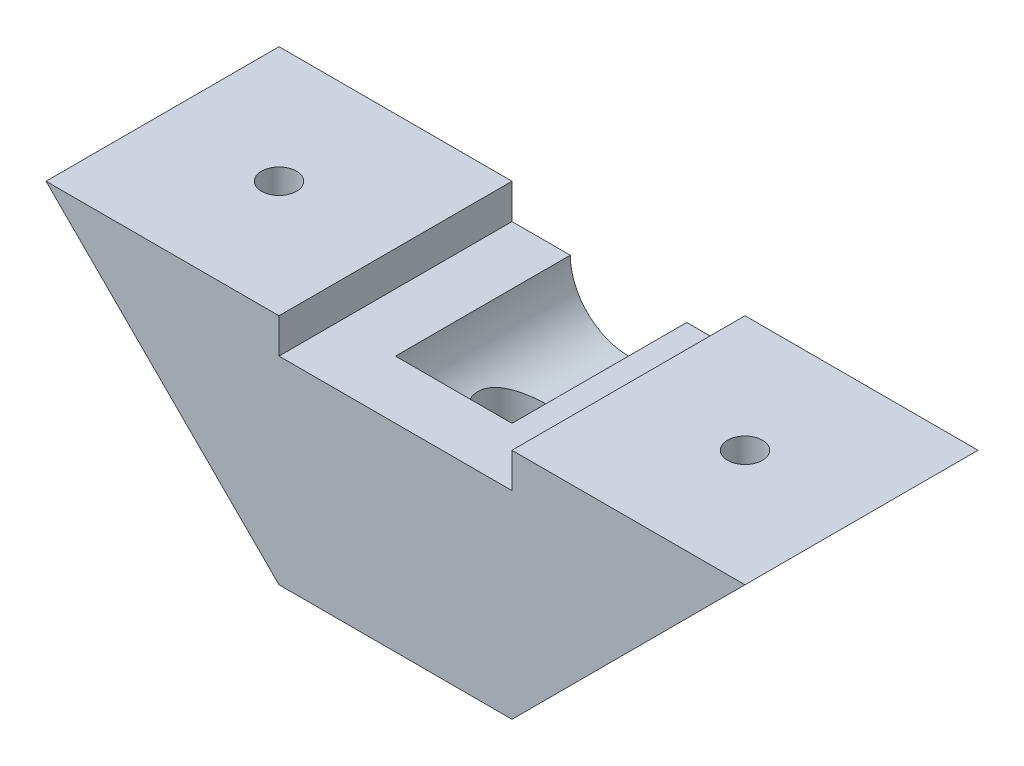
SolidWorks part; units mm, degrees
ref_plane "Plan de face" through (0, 0, 0) normal (0, 0, 1) x (1, 0, 0)
ref_plane "Plan de dessus" through (0, 0, 0) normal (0, 1, 0) x (1, 0, 0)
ref_plane "Plan de droite" through (0, 0, 0) normal (1, 0, 0) x (0, 0, -1)
sketch "Esquisse1" plane through (0, 0, 0) normal (0, 0, 1) x (1, 0, 0)
  line L0 (0, 20) -> (20, 0)
  line L1 (0, 0) -> (60, 0)
  line L2 (0, 0) -> (0, 60)
  line L3 (0, 60) -> (60, 60)
  line L4 (60, 0) -> (60, 60)
  line L5 (0, 0) -> (20, 0)
  line L6 (0, 0) -> (0, 20)
  line L7 (0, 20) -> (20, 20)
  line L8 (20, 0) -> (20, 20)
  line L9 (60, 0) -> (40, 0)
  line L10 (60, 0) -> (60, 20)
  line L11 (60, 20) -> (40, 20)
  line L12 (40, 0) -> (40, 20)
  line L13 (40, 0) -> (60, 20)
  line L15 (20, 0) -> (40, 0)
  line L16 (20, 0) -> (20, 17)
  line L17 (20, 17) -> (40, 17)
  line L18 (40, 0) -> (40, 17)
  circle A0 centre (30, 17) radius 5
  point P13 (30, 0)
  dimension "D8" = 10
  dimension "D1" = 60
  dimension "D2" = 60
  dimension "D3" = 20
  dimension "D4" = 20
  dimension "D5" = 20
  dimension "D6" = 20
  dimension "D7" = 17
extrude "Boss.-Extru.1" add sketch "Esquisse1" along normal blind 15 contours L0 L8 L7 | A0 L17 L8 L1 L12 | L12 L13 L11
sketch "Esquisse3" plane through (0, 0, 15) normal (0, 0, 1) x (1, 0, 0)
  line L0 (25, 17) -> (35, 17)
  line L9 (0, 20) -> (20, 0)
  line L10 (20, 0) -> (40, 0)
  line L11 (40, 0) -> (60, 20)
  line L12 (60, 20) -> (40, 20)
  line L13 (40, 20) -> (40, 17)
  line L14 (40, 17) -> (35, 17)
  line L15 (25, 17) -> (20, 17)
  line L16 (20, 17) -> (20, 20)
  line L17 (20, 20) -> (0, 20)
  line L18 (0, 20) -> (20, 0)
  line L19 (20, 0) -> (40, 0)
  line L20 (40, 0) -> (60, 20)
  line L21 (60, 20) -> (40, 20)
  line L22 (40, 20) -> (40, 17)
  line L23 (40, 17) -> (35, 17)
  line L24 (25, 17) -> (20, 17)
  line L25 (20, 17) -> (20, 20)
  line L26 (20, 20) -> (0, 20)
  arc A1 (25, 17) -> (35, 17) centre (30, 17) ccw
  arc A2 (25, 17) -> (35, 17) centre (30, 17) ccw
  line M11 (0, 20) -> (20, 0)
  line M12 (20, 0) -> (40, 0)
  line M13 (40, 0) -> (60, 20)
  line M14 (60, 20) -> (40, 20)
  line M15 (40, 20) -> (40, 17)
  line M16 (40, 17) -> (35, 17)
  arc M17 (35, 17) -> (25, 17) centre (30, 17) cw
  line M18 (25, 17) -> (20, 17)
  line M19 (20, 17) -> (20, 20)
  line M20 (20, 20) -> (0, 20)
  dimension "D1" = 0
extrude "Boss.-Extru.2" add sketch "Esquisse3" along normal blind 5 contours L0 M17 | M20 M11 M12 M13 M14 M15 M16 M17 M18 M19
sketch "Esquisse2" plane through (0, 20, 0) normal (0, 1, 0) x (1, 0, 0)
  line L1 (60, 0) -> (30, 0)
  line L2 (60, 0) -> (60, -10)
  line L3 (60, -10) -> (30, -10)
  line L4 (30, 0) -> (30, -10)
  circle A0 centre (30, -10) radius 1.6
  dimension "D3" = 3.2
  dimension "D1" = 10
  dimension "D2" = 30
extrude "Enlèv. mat.-Extru.1" cut sketch "Esquisse2" against normal blind 20 contours L3 A0 L4 | L4 A0 L3
sketch "Esquisse4" plane through (0, 20, 0) normal (0, 1, 0) x (1, 0, 0)
  circle A0 centre (30, -10) radius 1.6 construction
  circle A1 centre (30, -10) radius 1.6
  circle A2 centre (30, -10) radius 2.9
  dimension "D1" = 5.8
extrude "Enlèv. mat.-Extru.2" cut sketch "Esquisse4" against normal blind 12
sketch "Esquisse5" plane through (0, 20, 0) normal (0, 1, 0) x (1, 0, 0)
  line L0 (60, 0) -> (40, 0) construction
  line L1 (40, 0) -> (40, -20) construction
  line L2 (40, -20) -> (60, -20) construction
  line L3 (60, -20) -> (60, 0) construction
  line L4 (60, 0) -> (40, 0)
  line L5 (40, 0) -> (40, -20)
  line L6 (40, -20) -> (60, -20)
  line L7 (60, -20) -> (60, 0)
  line L8 (60, 0) -> (40, 0)
  line L9 (40, 0) -> (40, -20)
  line L10 (40, -20) -> (60, -20)
  line L11 (60, -20) -> (60, 0)
  line L12 (20, 0) -> (0, 0) construction
  line L13 (0, 0) -> (0, -20) construction
  line L14 (0, -20) -> (20, -20) construction
  line L15 (20, -20) -> (20, 0) construction
  line L16 (60, 0) -> (40, 0)
  line L17 (40, 0) -> (40, -20)
  line L18 (40, -20) -> (60, -20)
  line L19 (60, -20) -> (60, 0)
  line L20 (20, 0) -> (0, 0)
  line L21 (0, 0) -> (0, -20)
  line L22 (0, -20) -> (20, -20)
  line L23 (20, -20) -> (20, 0)
  line L24 (0, -20) -> (20, 0)
  line L25 (0, 0) -> (20, -20)
  line L26 (40, -20) -> (60, 0)
  line L27 (60, -20) -> (40, 0)
  circle A0 centre (10, -10) radius 1.5
  circle A1 centre (50, -10) radius 1.5
  dimension "D2" = 3
  dimension "D3" = 3
  dimension "D1" = 0
extrude "Enlèv. mat.-Extru.3" cut sketch "Esquisse5" against normal blind 12 contours L27 A1 L26 | L26 A1 L27 | L27 A1 L26 | L26 A1 L27 | L25 A0 L24 | L24 A0 L25 | L25 A0 L24 | L24 A0 L25
sketch "Esquisse7" plane through (0, 0, 0) normal (0, -1, 0) x (1, 0, 0)
  line L1 (10, 6.8823) -> (12.7, 8.4412)
  line L2 (12.7, 8.4412) -> (12.7, 11.5588)
  line L3 (12.7, 11.5588) -> (10, 13.1177)
  line L4 (10, 13.1177) -> (7.3, 11.5588)
  line L5 (7.3, 11.5588) -> (7.3, 8.4412)
  line L6 (7.3, 8.4412) -> (10, 6.8823)
  line L7 (50, 6.8823) -> (52.7, 8.4412)
  line L8 (52.7, 8.4412) -> (52.7, 11.5588)
  line L9 (52.7, 11.5588) -> (50, 13.1177)
  line L10 (50, 13.1177) -> (47.3, 11.5588)
  line L11 (47.3, 11.5588) -> (47.3, 8.4412)
  line L12 (47.3, 8.4412) -> (50, 6.8823)
  circle A0 centre (50, 10) radius 1.5 construction
  circle A1 centre (10, 10) radius 1.5 construction
  circle A2 centre (50, 10) radius 1.5
  circle A3 centre (10, 10) radius 1.5
  circle A4 centre (10, 10) radius 2.7 construction
  circle A5 centre (50, 10) radius 2.7 construction
  dimension "D1" = 5.4
  dimension "D2" = 5.4
extrude "Enlèv. mat.-Extru.5" cut sketch "Esquisse7" against normal blind 15
